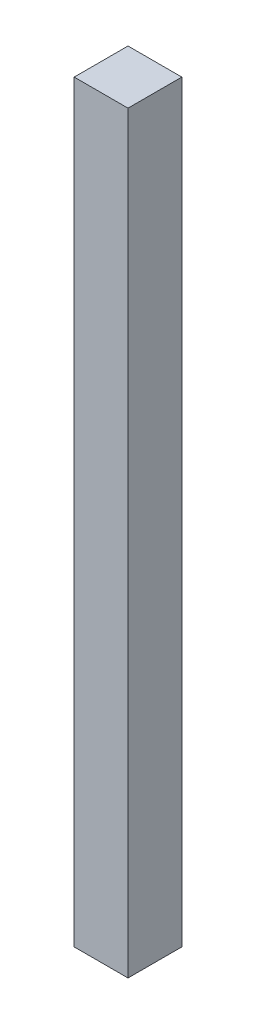
SolidWorks part; units mm, degrees
ref_plane "Front Plane" through (0, 0, 0) normal (0, 0, 1) x (1, 0, 0)
ref_plane "Top Plane" through (0, 0, 0) normal (0, 1, 0) x (1, 0, 0)
ref_plane "Right Plane" through (0, 0, 0) normal (1, 0, 0) x (0, 0, -1)
sketch "Sketch1" plane through (0, 0, 0) normal (0, 1, 0) x (1, 0, 0)
  line L1 (0, 0) -> (10, 0)
  line L2 (0, 0) -> (0, 10)
  line L3 (0, 10) -> (10, 10)
  line L4 (10, 0) -> (10, 10)
  dimension "D1" = 10
  dimension "w" = 10
extrude "Boss-Extrude1" add sketch "Sketch1" along normal blind 140
